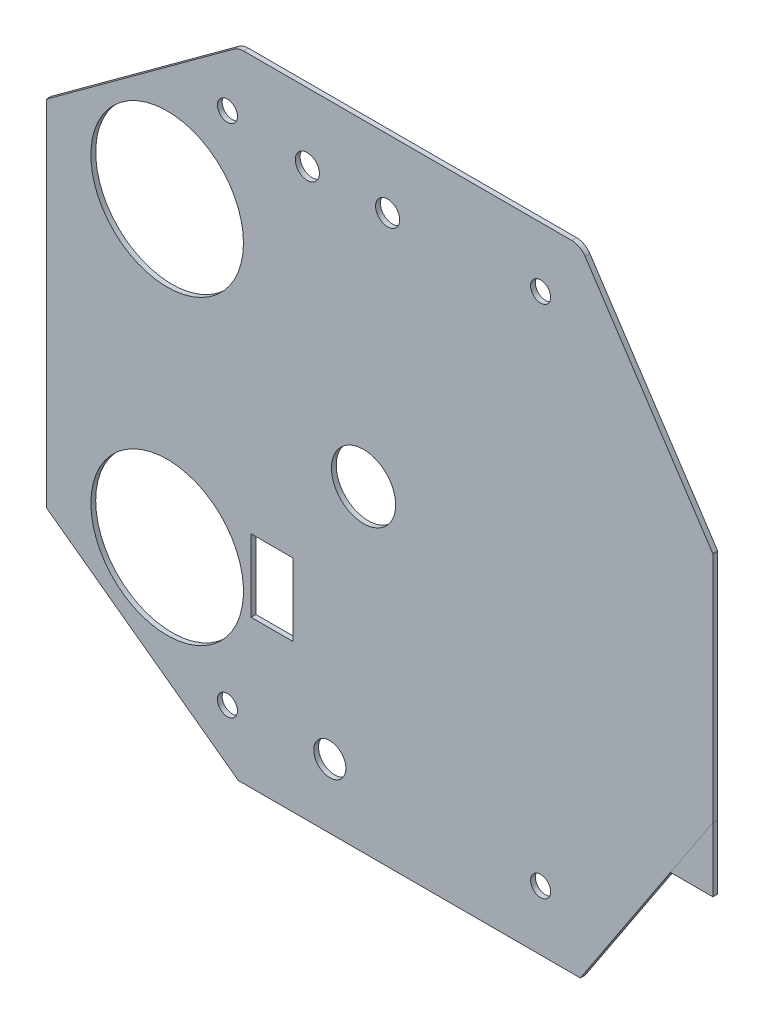
SolidWorks part; units mm, degrees
ref_plane "Plan de face" through (0, 0, 0) normal (0, 0, 1) x (1, 0, 0)
ref_plane "Plan de dessus" through (0, 0, 0) normal (0, 1, 0) x (1, 0, 0)
ref_plane "Plan de droite" through (0, 0, 0) normal (1, 0, 0) x (0, 0, -1)
sketch "Esquisse3" plane through (0, 0, 0) normal (0, 0, 1) x (1, 0, 0)
  line L0 (23.3839, 39.1146) -> (0, 22.0214)
  line L1 (83, -14.5) -> (66.5, -39.5)
  line L2 (0, -22.0214) -> (0, 22.0214)
  line L3 (24.5641, 39.5) -> (65.4237, 39.5)
  line L4 (83, -14.5) -> (83, 14.5)
  line L5 (83, 14.5) -> (67.0929, 38.6017)
  line L6 (23.9111, -39.5) -> (66.5, -39.5)
  line L7 (-5.6809, 0) -> (87.238, 0) construction
  line L8 (23.9111, -39.5) -> (0, -22.0214)
  circle A0 centre (15.0506, 18.7783) radius 9.5
  circle A1 centre (39.5, 0) radius 4
  circle A2 centre (22.5506, 32.05) radius 1.25
  circle A3 centre (61.5506, 32.05) radius 1.25
  circle A4 centre (61.5506, -32.05) radius 1.25
  circle A5 centre (22.5506, -32.05) radius 1.25
  circle A6 centre (15.0506, -18.7783) radius 9.5
  arc A7 (65.4237, 39.5) -> (67.0929, 38.6017) centre (65.4237, 37.5) cw
  arc A8 (23.3839, 39.1146) -> (24.5641, 39.5) centre (24.5641, 37.5) cw
  point P25 (83, 0)
  point P27 (0, 0)
  point P29 (66.5, 39.5)
  point P32 (23.9111, 39.5)
  dimension "D7" = 19
  dimension "D10" = 8
  dimension "D12" = 2.5
  dimension "D11" = 2
  dimension "D2" = 83
  dimension "D3" = 39
  dimension "D4" = 25
  dimension "D5" = 39.5
  dimension "D6" = 39.5
  dimension "D9" = 11.5
  dimension "D13" = 32.05
extrude "Extrusion1" add sketch "Esquisse3" along normal blind 0.6
sketch "Esquisse4" plane through (0, 0, 0.6) normal (0, 0, 1) x (1, 0, 0)
  line L0 (83, -14.5) -> (83, -22.5)
  line L1 (83, -22.5) -> (77.72, -22.5)
  line L2 (66.5, -39.5) -> (83, -14.5) construction
  line L3 (77.72, -22.5) -> (83, -14.5)
  dimension "D1" = 37
extrude "Extrusion2" add sketch "Esquisse4" against normal blind 0.6 separate body
sketch "Esquisse5" plane through (0, 0, 0.6) normal (0, 0, 1) x (1, 0, 0)
  line L0 (65.4237, 39.5) -> (24.5641, 39.5) construction
  line L1 (25.5, -12.1) -> (30.7, -12.1)
  line L2 (25.5, -12.1) -> (25.5, -21.1)
  line L3 (25.5, -21.1) -> (30.7, -21.1)
  line L4 (30.7, -12.1) -> (30.7, -21.1)
  line L6 (0, 22.0214) -> (0, -22.0214) construction
  line L7 (23.9111, -39.5) -> (66.5, -39.5) construction
  circle A0 centre (35.3006, -31.5) radius 2
  circle A1 centre (32.5, 31) radius 1.5
  circle A3 centre (42.5, 31) radius 1.5
  circle A6 centre (22.5506, -32.05) radius 1.25 construction
  dimension "D1" = 3
  dimension "D4" = 9
  dimension "D8" = 4
  dimension "D9" = 12.75
  dimension "D2" = 8.5
  dimension "D3" = 32.5
  dimension "D5" = 5.2
  dimension "D6" = 18.4
  dimension "D7" = 25.5
  dimension "D10" = 8
extrude "Extrusion3" cut sketch "Esquisse5" against normal blind 0.6
